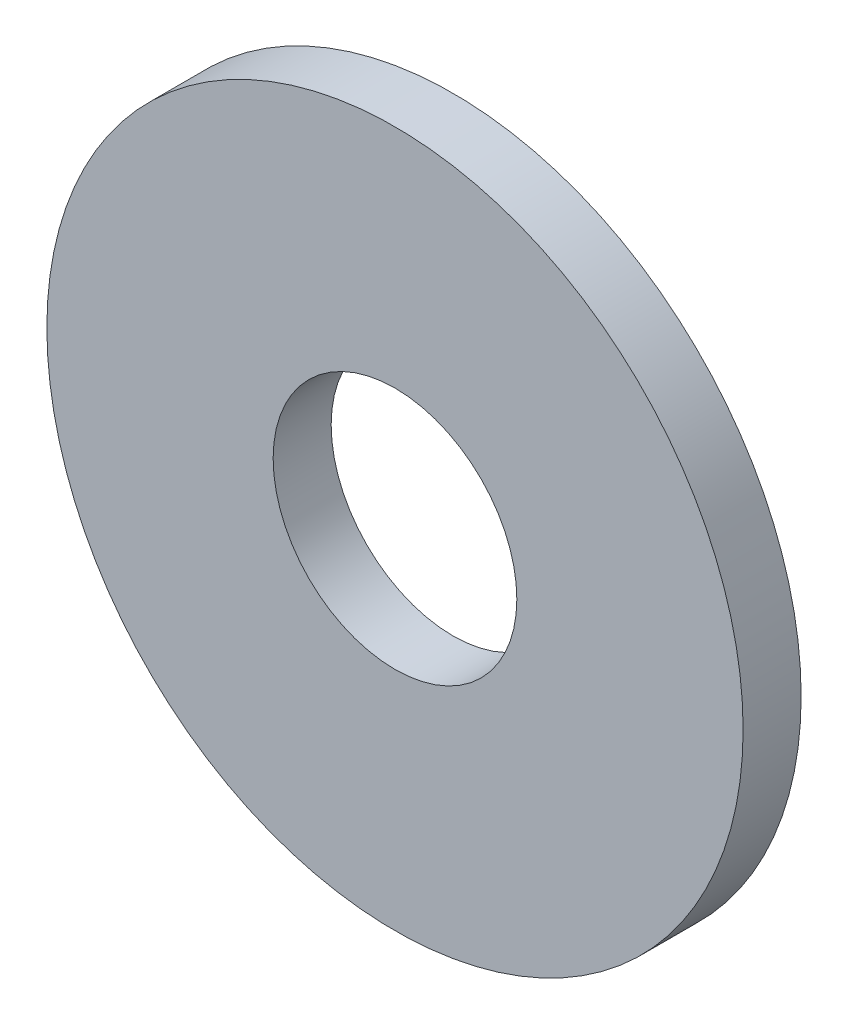
SolidWorks part; units mm, degrees
material "Plain Carbon Steel"
ref_plane "Front Plane" through (0, 0, 0) normal (0, 0, 1) x (1, 0, 0)
ref_plane "Top Plane" through (0, 0, 0) normal (0, 1, 0) x (1, 0, 0)
ref_plane "Right Plane" through (0, 0, 0) normal (1, 0, 0) x (0, 0, -1)
sketch "Sketch1" plane through (0, 0, 0) normal (1, 0, 0) x (0, 0, -1)
  line L0 (0, -15) -> (0, 15) construction
  line L1 (0, -5.25) -> (0, 5.25) construction
  line L2 (-1.25, 0) -> (1.25, 0) construction
  point P4 (0, 0)
  point P8 (0, 0)
  point P11 (0, 0)
sketch "Sketch2" plane through (0, 0, 0) normal (0, 0, 1) x (1, 0, 0)
  circle A0 centre (0, 0) radius 15
  circle A1 centre (0, 0) radius 5.25
extrude "Boss-Extrude1" add sketch "Sketch2" along normal mid plane 2.5
equation "\"D1@Boss-Extrude1\" = \"Thickness@Sketch1\""
